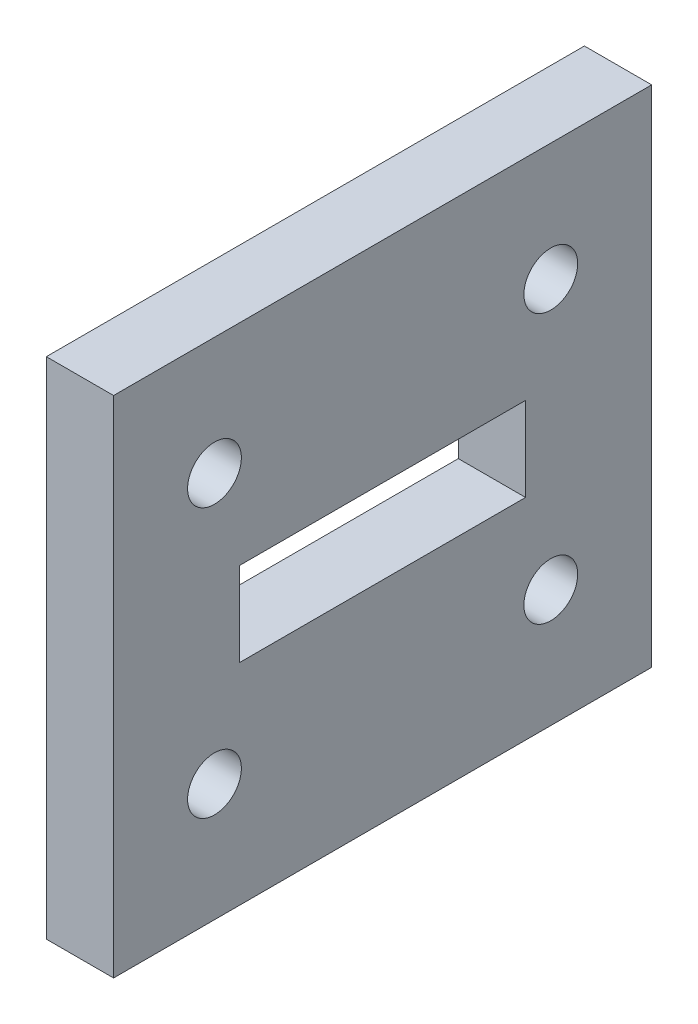
SolidWorks part; units mm, degrees
ref_plane "Спереди" through (0, 0, 0) normal (0, 0, 1) x (1, 0, 0)
ref_plane "Сверху" through (0, 0, 0) normal (0, 1, 0) x (1, 0, 0)
ref_plane "Справа" through (0, 0, 0) normal (1, 0, 0) x (0, 0, -1)
ref_plane "Плоскость4" through (15.4739, 0, 0) normal (1, 0, 0) x (0, 0, -1)
sketch "Эскиз1" plane through (15.4739, 0, 0) normal (1, 0, 0) x (0, 0, -1)
  line L4 (-13.2363, 38.4936) -> (-13.2363, 8.4936)
  line L5 (-13.2363, 38.4936) -> (-13.2363, 8.4936)
  line L6 (-13.2363, 8.4936) -> (18.7637, 8.4936)
  line L7 (-13.2363, 8.4936) -> (18.7637, 8.4936)
  line L8 (18.7637, 8.4936) -> (18.7637, 38.4936)
  line L9 (18.7637, 8.4936) -> (18.7637, 38.4936)
  line L10 (18.7637, 38.4936) -> (-13.2363, 38.4936)
  line L11 (18.7637, 38.4936) -> (-13.2363, 38.4936)
  circle A0 centre (-7.2363, 31.4936) radius 1.6 construction
  circle A1 centre (12.7637, 31.4936) radius 1.6 construction
  circle A2 centre (-7.2363, 15.4936) radius 1.6 construction
  circle A3 centre (12.7637, 15.4936) radius 1.6 construction
  circle A4 centre (-7.2363, 31.4936) radius 1.6
  circle A5 centre (12.7637, 31.4936) radius 1.6
  circle A6 centre (-7.2363, 15.4936) radius 1.6
  circle A7 centre (12.7637, 15.4936) radius 1.6
  dimension "D1" = 0
extrude "Бобышка-Вытянуть1" add sketch "Эскиз1" along normal blind 4
sketch "Sketch2" plane through (15.4739, 0, 0) normal (-1, 0, 0) x (0, 0, 1)
  line L0 (-11.2637, 25.9936) -> (-11.2637, 20.9936)
  line L1 (-11.2637, 25.9936) -> (5.7363, 25.9936)
  line L2 (-11.2637, 20.9936) -> (5.7363, 20.9936)
  line L3 (5.7363, 25.9936) -> (5.7363, 20.9936)
  line L4 (-12.7637, 31.4936) -> (7.2363, 31.4936) construction
  line L5 (-12.7637, 31.4936) -> (-12.7637, 15.4936) construction
  line L6 (7.2363, 31.4936) -> (7.2363, 15.4936) construction
  line L7 (-12.7637, 15.4936) -> (7.2363, 15.4936) construction
  line L8 (-2.7637, 31.4936) -> (-2.7637, 15.4936) construction
  line L9 (-2.7637, 25.9936) -> (-2.7637, 20.9936) construction
  line L10 (7.2363, 23.4936) -> (-12.7637, 23.4936) construction
  line L11 (5.7363, 23.4936) -> (-11.2637, 23.4936) construction
  circle A0 centre (-12.7637, 15.4936) radius 1.6 construction
  circle A1 centre (-12.7637, 15.4936) radius 1.6 construction
  dimension "D1" = 17
  dimension "D2" = 5
extrude "Cut-Extrude2" cut sketch "Sketch2" against normal through all
